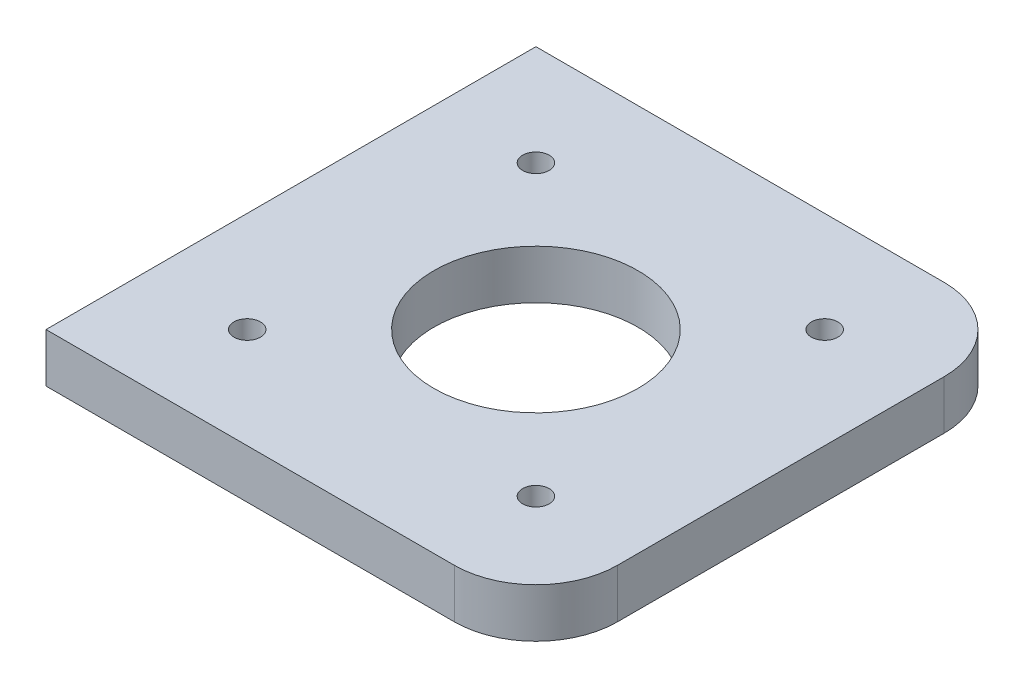
SolidWorks part; units mm, degrees
ref_plane "Front Plane" through (0, 0, 0) normal (0, 0, 1) x (1, 0, 0)
ref_plane "Top Plane" through (0, 0, 0) normal (0, 1, 0) x (1, 0, 0)
ref_plane "Right Plane" through (0, 0, 0) normal (1, 0, 0) x (0, 0, -1)
sketch "Sketch1" plane through (0, 0, 0) normal (0, 1, 0) x (1, 0, 0)
  line L0 (-12.32, 47.68) -> (47.68, -12.32) construction
  line L1 (0, 0) -> (35.36, 0) construction
  line L2 (0, 0) -> (0, 35.36) construction
  line L3 (0, 35.36) -> (35.36, 35.36) construction
  line L4 (35.36, 0) -> (35.36, 35.36) construction
  line L5 (-12.32, 47.68) -> (47.68, 47.68)
  line L6 (-12.32, 47.68) -> (-12.32, -12.32)
  line L7 (-12.32, -12.32) -> (47.68, -12.32)
  line L8 (47.68, 47.68) -> (47.68, -12.32)
  line L9 (-12.32, -12.32) -> (47.68, 47.68) construction
  line L10 (0, 35.36) -> (35.36, 0) construction
  line L11 (35.36, 35.36) -> (0, 0) construction
  circle A0 centre (0, 35.36) radius 1.625
  circle A1 centre (35.36, 35.36) radius 1.625
  circle A2 centre (35.36, 0) radius 1.625
  circle A3 centre (0, 0) radius 1.625
  circle A4 centre (17.68, 17.68) radius 12.5
  point P13 (17.68, 17.68)
  point P14 (17.68, 17.68)
  dimension "D3" = 3.25
  dimension "D4" = 3.25
  dimension "D5" = 3.25
  dimension "D6" = 3.25
  dimension "D9" = 25
  dimension "D1" = 35.36
  dimension "D2" = 35.36
  dimension "D7" = 60
  dimension "D8" = 60
extrude "Boss-Extrude1" add sketch "Sketch1" along normal blind 6
fillet "Fillet1" radius 10 2 edges at (47.68, 3, -47.68) (47.68, 3, 12.32)
